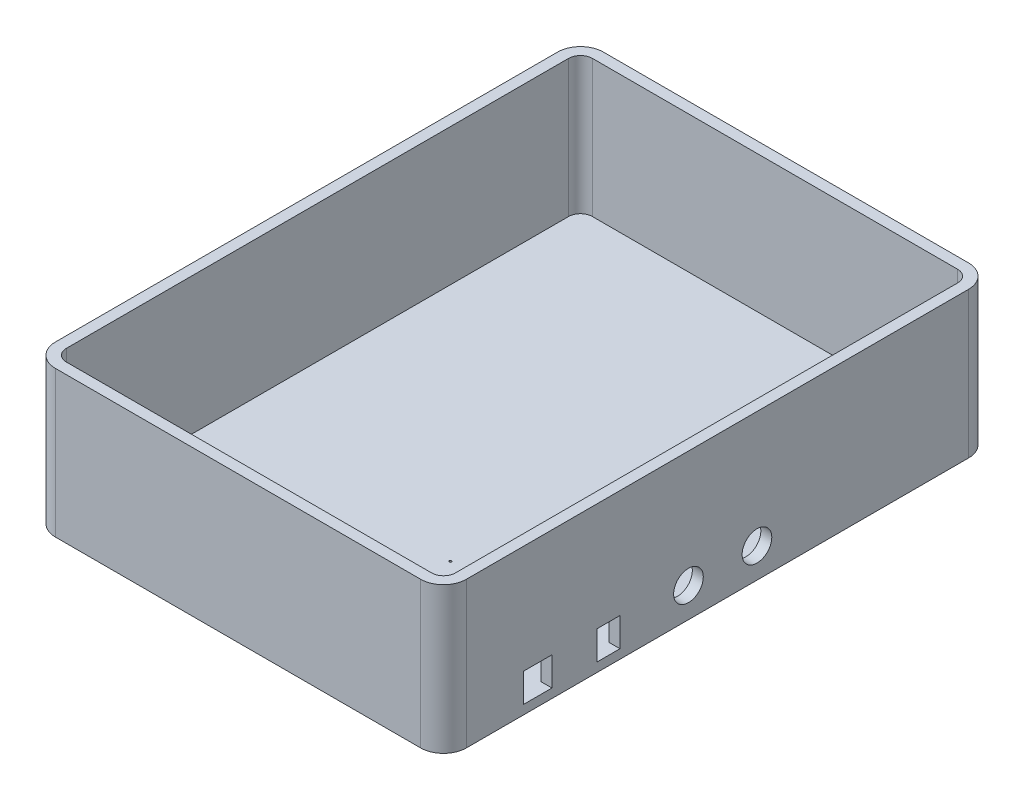
SolidWorks part; units mm, degrees
ref_plane "Front Plane" through (0, 0, 0) normal (0, 0, 1) x (1, 0, 0)
ref_plane "Top Plane" through (0, 0, 0) normal (0, 1, 0) x (1, 0, 0)
ref_plane "Right Plane" through (0, 0, 0) normal (1, 0, 0) x (0, 0, -1)
sketch "Sketch1" plane through (0, 0, 0) normal (0, 1, 0) x (1, 0, 0)
  line L0 (0, 0) -> (180, 0)
  line L1 (0, 0) -> (0, 240)
  line L2 (0, 240) -> (180, 240)
  line L3 (180, 0) -> (180, 240)
  dimension "D1" = 180
  dimension "D2" = 240
extrude "Boss-Extrude1" add sketch "Sketch1" along normal blind 4
fillet "Fillet1" radius 10 4 edges at (0, 2, -240) (180, 2, -240) (0, 2, 0) (180, 2, 0)
sketch "Sketch2" plane through (0, 4, 0) normal (0, 1, 0) x (1, 0, 0)
  line L0 (170, 235.2) -> (10, 235.2)
  line L1 (4.8, 230) -> (4.8, 10)
  line L2 (10, 4.8) -> (170, 4.8)
  line L3 (175.2, 10) -> (175.2, 230)
  line L4 (170, 240) -> (10, 240)
  line L5 (0, 230) -> (0, 10)
  line L6 (10, 0) -> (170, 0)
  line L7 (180, 10) -> (180, 230)
  line L8 (170, 240) -> (10, 240)
  line L9 (0, 230) -> (0, 10)
  line L10 (10, 0) -> (170, 0)
  line L11 (180, 10) -> (180, 230)
  arc A0 (10, 235.2) -> (4.8, 230) centre (10, 230) ccw
  arc A1 (4.8, 10) -> (10, 4.8) centre (10, 10) ccw
  arc A2 (170, 4.8) -> (175.2, 10) centre (170, 10) ccw
  arc A3 (175.2, 230) -> (170, 235.2) centre (170, 230) ccw
  arc A4 (10, 240) -> (0, 230) centre (10, 230) ccw
  arc A5 (0, 10) -> (10, 0) centre (10, 10) ccw
  arc A6 (170, 0) -> (180, 10) centre (170, 10) ccw
  arc A7 (180, 230) -> (170, 240) centre (170, 230) ccw
  arc A8 (10, 240) -> (0, 230) centre (10, 230) ccw
  arc A9 (0, 10) -> (10, 0) centre (10, 10) ccw
  arc A10 (170, 0) -> (180, 10) centre (170, 10) ccw
  arc A11 (180, 230) -> (170, 240) centre (170, 230) ccw
  dimension "D1" = 0
  dimension "D2" = 4.8
extrude "Boss-Extrude2" add sketch "Sketch2" along normal blind 60
sketch "Sketch3" plane through (0, 4, 0) normal (0, 1, 0) x (1, 0, 0)
  line L0 (175.2, 10) -> (175.2, 230) construction
  line L1 (109.7, 73.3) -> (109.7, 45.3) construction
  line L2 (175.2, 80.3) -> (109.7, 80.3) construction
  line L3 (175.2, 10) -> (175.2, 230) construction
  line L4 (10, 4.8) -> (170, 4.8) construction
  circle A0 centre (159.96, 29.8) radius 0.5
  circle A2 centre (109.7, 45.3) radius 0.5
  circle A3 centre (109.7, 73.3) radius 0.5
  dimension "D2" = 1
  dimension "D1" = 15.24
  dimension "D3" = 65.5
  dimension "D4" = 50.5
  dimension "D5" = 7
  dimension "D6" = 25
  dimension "D7" = 35
extrude "Cut-Extrude1" cut sketch "Sketch3" against normal through all both and the other way through all
sketch "Sketch4" plane through (0, 4, 0) normal (0, 1, 0) x (1, 0, 0)
  line L0 (167.7, 41.25) -> (175.2, 41.25) construction
  line L1 (175.2, 10) -> (175.2, 230) construction
  line L2 (159.96, 29.8) -> (175.2, 29.8) construction
  line L3 (182.7, 47.5) -> (167.7, 47.5)
  line L4 (182.7, 47.5) -> (182.7, 35)
  line L5 (182.7, 35) -> (167.7, 35)
  line L6 (167.7, 47.5) -> (167.7, 35)
  line L7 (182.7, 47.5) -> (167.7, 35) construction
  line L8 (182.7, 35) -> (167.7, 47.5) construction
  line L9 (175.2, 72.29) -> (159.96, 72.29) construction
  line L11 (185.2, 77.29) -> (165.2, 77.29)
  line L12 (185.2, 77.29) -> (185.2, 67.29)
  line L13 (185.2, 67.29) -> (165.2, 67.29)
  line L14 (165.2, 77.29) -> (165.2, 67.29)
  line L15 (185.2, 77.29) -> (165.2, 67.29) construction
  line L16 (185.2, 67.29) -> (165.2, 77.29) construction
  dimension "D1" = 12.5
  dimension "D2" = 11.45
  dimension "D3" = 15
  dimension "D4" = 42.49
  dimension "D5" = 20
  dimension "D6" = 10
extrude "Cut-Extrude2" cut sketch "Sketch4" along normal blind 12.6
sketch "Sketch5" plane through (180, 0, 0) normal (1, 0, 0) x (0, 0, -1)
  line L0 (10, 0) -> (230, 0) construction
  line L1 (77.29, 4) -> (77.29, 16.6) construction
  circle A0 centre (107.29, 13) radius 6.5
  circle A1 centre (137.29, 13) radius 6.5
  dimension "D1" = 13
  dimension "D2" = 13
  dimension "D3" = 30
  dimension "D4" = 30
extrude "Cut-Extrude3" cut sketch "Sketch5" against normal blind 12.6
